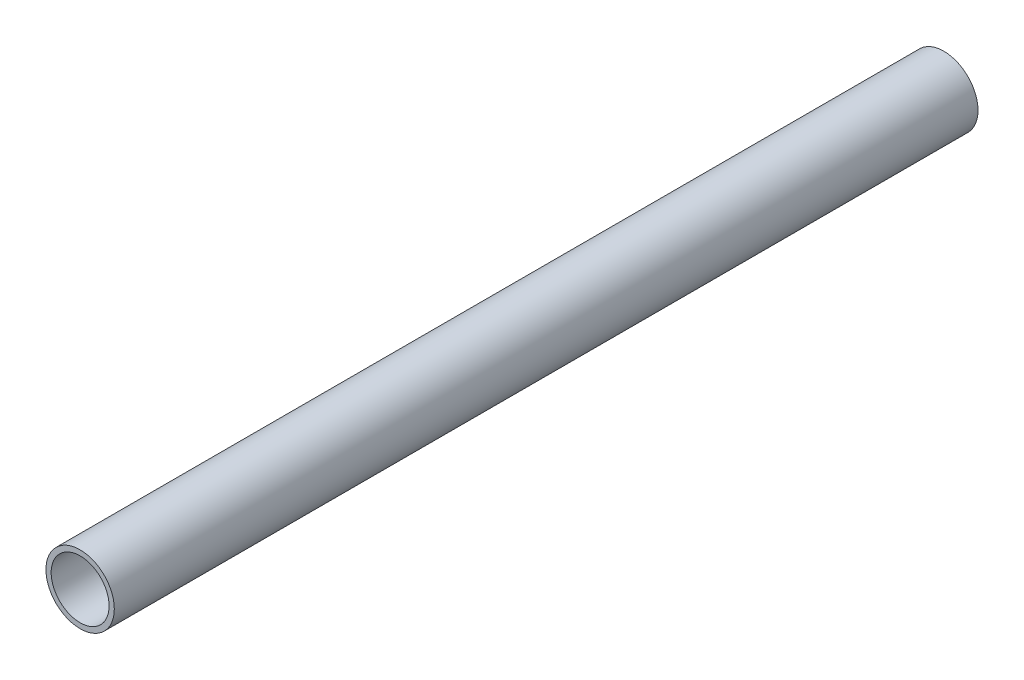
SolidWorks part; units mm, degrees
ref_plane "Front Plane" through (0, 0, 0) normal (0, 0, 1) x (1, 0, 0)
ref_plane "Top Plane" through (0, 0, 0) normal (0, 1, 0) x (1, 0, 0)
ref_plane "Right Plane" through (0, 0, 0) normal (1, 0, 0) x (0, 0, -1)
sketch "Sketch2" plane through (0, 0, 0) normal (1, 0, 0) x (0, 0, -1)
  line L0 (-241.3, 24.13) -> (-241.3, -24.13) construction
  line L1 (304.8, -24.13) -> (-304.8, -24.13)
  line L2 (304.8, -24.13) -> (304.8, 24.13)
  line L3 (304.8, 24.13) -> (-304.8, 24.13)
  line L4 (-304.8, -24.13) -> (-304.8, 24.13)
  line L5 (304.8, -24.13) -> (-304.8, 24.13) construction
  line L6 (304.8, 24.13) -> (-304.8, -24.13) construction
  line L7 (241.3, 24.13) -> (241.3, -24.13) construction
  point P0 (0, 0)
  point P6 (-304.8, 20.447)
  point P11 (-304.8, -20.447)
  dimension "Rail OD" = 48.26
  dimension "Wall Thickness" = 3.683
  dimension "Length" = 609.6
  dimension "D1" = 63.5
  dimension "D2" = 63.5
  dimension "D3" = 3.683
sketch "Sketch1" plane through (0, 0, 0) normal (0, 0, 1) x (1, 0, 0)
  line L0 (24.13, 0) -> (20.447, 0) construction
  circle A0 centre (0, 0) radius 24.13
  dimension "D1" = 3.683
extrude "Extrude-Thin1" add sketch "Sketch1" along normal mid plane 609.6 thin thin type one direction reverse wall 3.683
equation "\"D1@Sketch1\"=\"Wall Thickness@Sketch2\""
equation "\"D5@Extrude-Thin1\" = \"Wall Thickness@Sketch2\""
equation "\"D1@Extrude-Thin1\" = \"Length@Sketch2\""
equation "\"D2@Sketch2\"=\"D1@Sketch2\""
equation "\"D3@Sketch2\"= \"Wall Thickness@Sketch2\""
